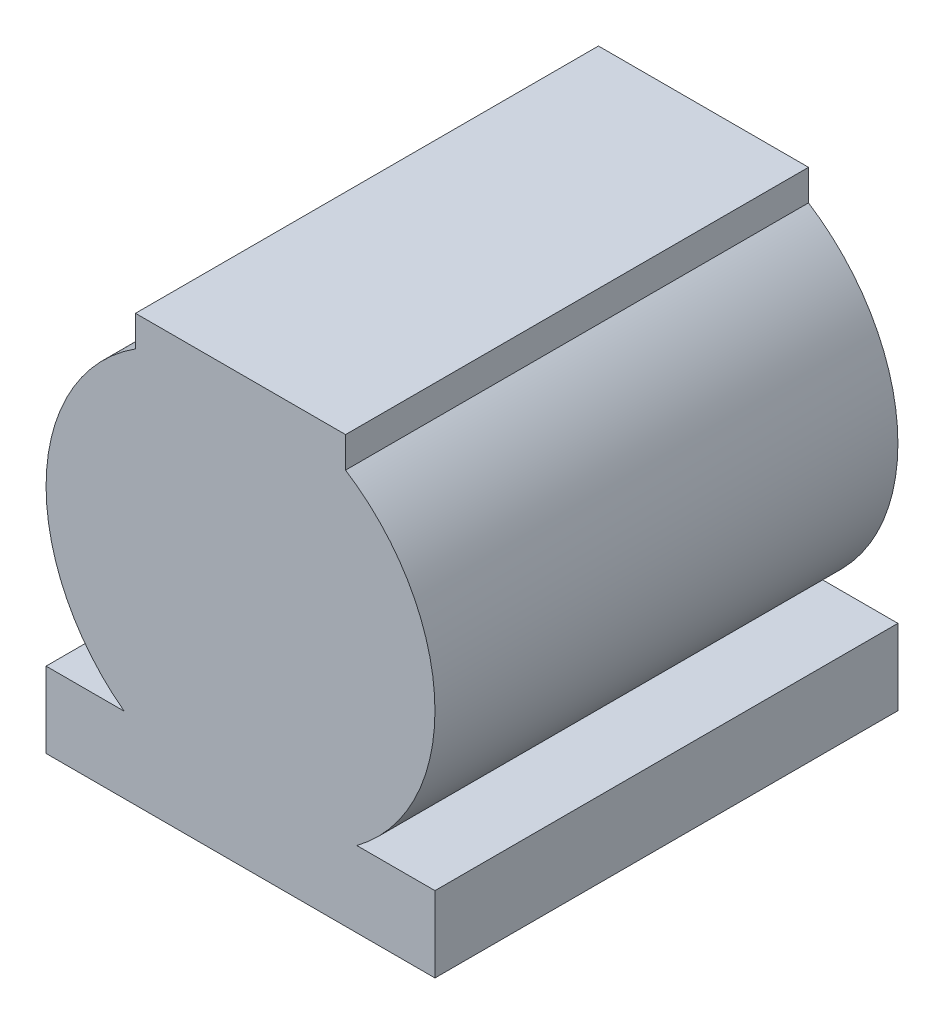
SolidWorks part; units mm, degrees
ref_plane "Спереди" through (0, 0, 0) normal (0, 0, 1) x (1, 0, 0)
ref_plane "Сверху" through (0, 0, 0) normal (0, 1, 0) x (1, 0, 0)
ref_plane "Справа" through (0, 0, 0) normal (1, 0, 0) x (0, 0, -1)
sketch "Эскиз1" plane through (0, 0, 0) normal (0, 1, 0) x (1, 0, 0)
  line L1 (52.5, -62.5) -> (-52.5, -62.5)
  line L2 (52.5, -62.5) -> (52.5, 62.5)
  line L3 (52.5, 62.5) -> (-52.5, 62.5)
  line L4 (-52.5, -62.5) -> (-52.5, 62.5)
  line L5 (52.5, -62.5) -> (-52.5, 62.5) construction
  line L6 (52.5, 62.5) -> (-52.5, -62.5) construction
  point P0 (0, 0)
  dimension "D1" = 125
  dimension "D2" = 105
extrude "Бобышка-Вытянуть1" add sketch "Эскиз1" along normal blind 115
sketch "Эскиз2" plane through (0, 0, 62.5) normal (0, 0, 1) x (1, 0, 0)
  line L0 (-28.361, 106.6804) -> (-28.361, 115)
  line L1 (-52.5, 115) -> (52.5, 115) construction
  line L3 (28.361, 115) -> (28.361, 106.6804)
  line L4 (31.4086, 20.4316) -> (52.5, 20.4316)
  line L5 (52.5, 115) -> (52.5, 0) construction
  line L6 (52.5, 20.4316) -> (52.5, 115)
  line L7 (52.5, 115) -> (28.361, 115)
  line L8 (-31.4086, 20.4316) -> (-52.5, 20.4316)
  line L9 (-52.5, 115) -> (-52.5, 0) construction
  line L10 (-52.5, 20.4316) -> (-52.5, 115)
  line L11 (-52.5, 115) -> (-28.361, 115)
  arc A0 (31.4086, 20.4316) -> (28.361, 106.6804) centre (0, 62.5) ccw
  arc A1 (-28.361, 106.6804) -> (-31.4086, 20.4316) centre (0, 62.5) ccw
  line M7 (52.5, 0) -> (52.5, 115)
  line M8 (52.5, 115) -> (-52.5, 115)
  line M9 (-52.5, 115) -> (-52.5, 0)
extrude "Вырез-Вытянуть1" cut sketch "Эскиз2" against normal through all both and the other way through all contours A1 L0 M8 M9 | A1 L10 L8 | A0 L4 M7 | A0 L6 L3 M8
